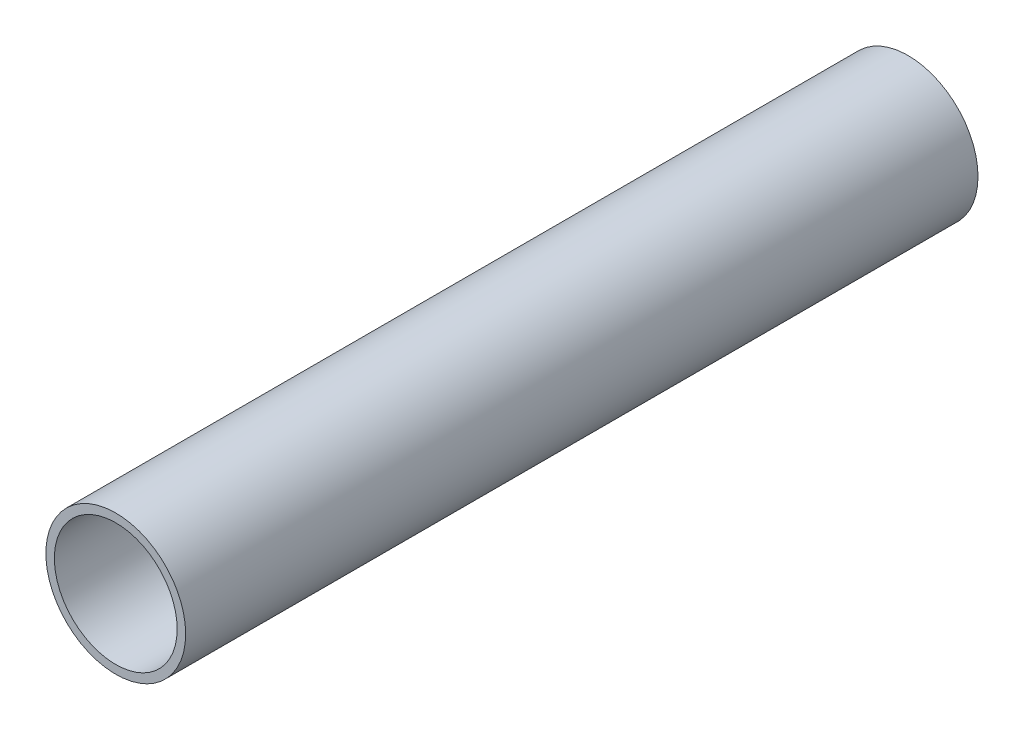
SolidWorks part; units mm, degrees
ref_plane "Front Plane" through (0, 0, 0) normal (0, 0, 1) x (1, 0, 0)
ref_plane "Top Plane" through (0, 0, 0) normal (0, 1, 0) x (1, 0, 0)
ref_plane "Right Plane" through (0, 0, 0) normal (1, 0, 0) x (0, 0, -1)
sketch "Sketch1" plane through (0, 0, 0) normal (0, 0, 1) x (1, 0, 0)
  circle A0 centre (0, 0) radius 12.35
  circle A1 centre (0, 0) radius 10.85
  dimension "D1" = 24.7
  dimension "D2" = 1.5
extrude "Boss-Extrude1" add sketch "Sketch1" along normal blind 140
